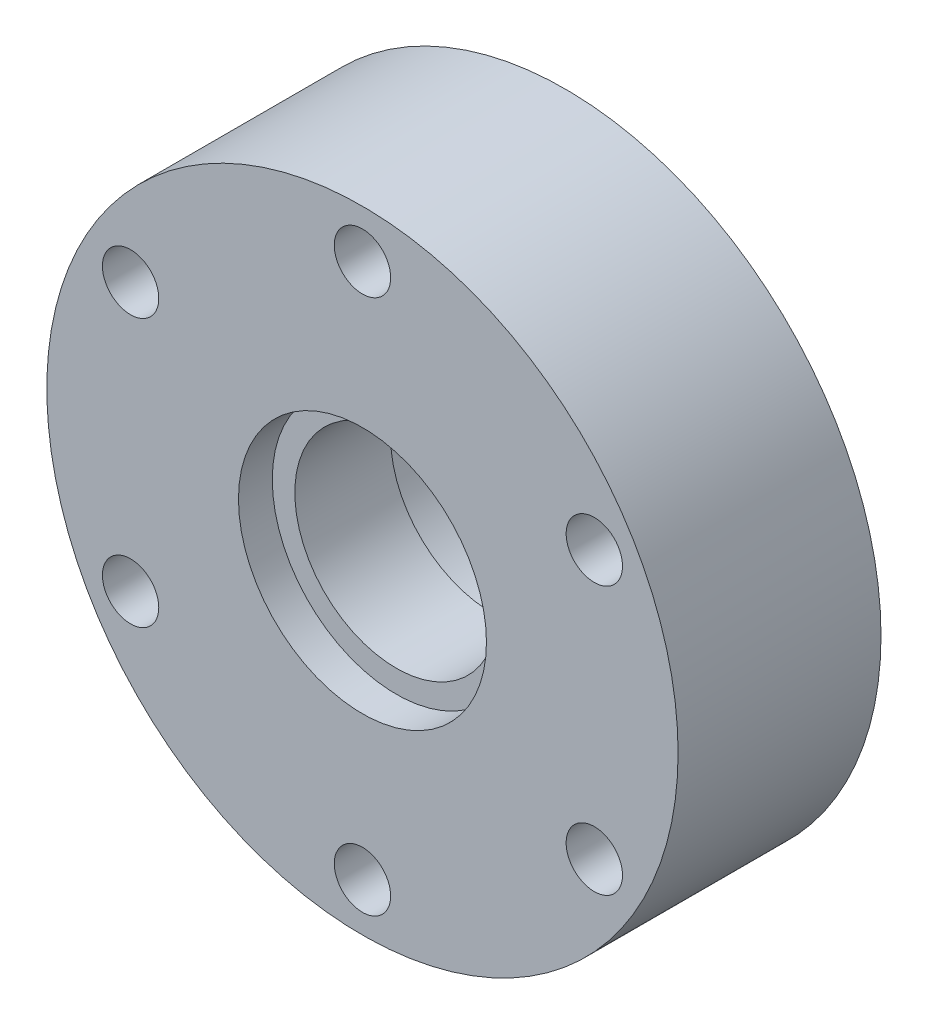
SolidWorks part; units mm, degrees
material "Polybutadiene (PB)"
ref_plane "Front Plane" through (0, 0, 0) normal (0, 0, 1) x (1, 0, 0)
ref_plane "Top Plane" through (0, 0, 0) normal (0, 1, 0) x (1, 0, 0)
ref_plane "Right Plane" through (0, 0, 0) normal (1, 0, 0) x (0, 0, -1)
sketch "Sketch1" plane through (0, 0, 0) normal (0, 0, 1) x (1, 0, 0)
  circle A0 centre (0, 0) radius 28
  dimension "D1" = 56
extrude "Boss-Extrude1" add sketch "Sketch1" along normal mid plane 18
sketch "Sketch2" plane through (0, 0, 9) normal (0, 0, 1) x (1, 0, 0)
  circle A0 centre (0, 0) radius 11
extrude "Cut-Extrude1" cut sketch "Sketch2" against normal blind 3
sketch "Sketch3" plane through (0, 0, 6) normal (0, 0, 1) x (1, 0, 0)
  circle A0 centre (0, 0) radius 9
extrude "Cut-Extrude2" cut sketch "Sketch3" against normal through all
sketch "Sketch4" plane through (0, 0, -9) normal (0, 0, -1) x (-1, 0, 0)
  circle A0 centre (0, 0) radius 11
extrude "Cut-Extrude3" cut sketch "Sketch4" against normal blind 6.5
sketch "草圖1" plane through (0, 0, 9) normal (0, 0, 1) x (1, 0, 0)
  line L0 (0, 0) -> (0, 23.75) construction
  circle A0 centre (0, 23.75) radius 2.5
  dimension "D1" = 5
  dimension "D2" = 23.75
extrude "除料-伸長1" cut sketch "草圖1" against normal through all
pattern_circular "環狀複製排列1" count 6 over 360 about axis through (0, 0, 0) along (0, 0, 1) of "除料-伸長1"
